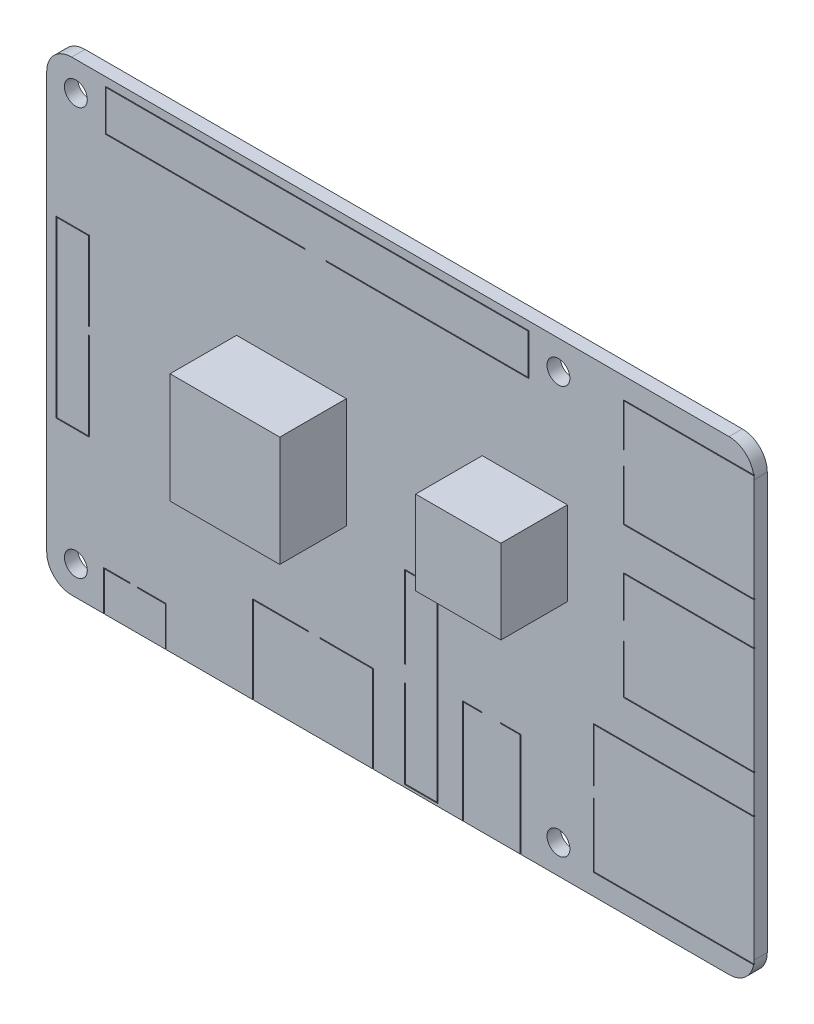
SolidWorks part; units mm, degrees
ref_plane "Front Plane" through (0, 0, 0) normal (0, 0, 1) x (1, 0, 0)
ref_plane "Top Plane" through (0, 0, 0) normal (0, 1, 0) x (1, 0, 0)
ref_plane "Right Plane" through (0, 0, 0) normal (1, 0, 0) x (0, 0, -1)
sketch "Sketch1" plane through (0, 0, 0) normal (0, 0, 1) x (1, 0, 0)
  line L1 (-39.5, -28) -> (39.5, -28)
  line L2 (-42.5, -25) -> (-42.5, 25)
  line L3 (-39.5, 28) -> (39.5, 28)
  line L4 (42.5, -25) -> (42.5, 25)
  line L5 (-42.5, -28) -> (42.5, 28) construction
  line L6 (-42.5, 28) -> (42.5, -28) construction
  arc A0 (-39.5, -28) -> (-42.5, -25) centre (-39.5, -25) cw
  arc A1 (39.5, -28) -> (42.5, -25) centre (39.5, -25) ccw
  arc A2 (39.5, 28) -> (42.5, 25) centre (39.5, 25) cw
  arc A3 (-42.5, 25) -> (-39.5, 28) centre (-39.5, 25) cw
  circle A4 centre (-39, 24.5) radius 1.375
  circle A5 centre (-39, -24.5) radius 1.375
  circle A6 centre (19, 24.5) radius 1.375
  circle A7 centre (19, -24.5) radius 1.375
  point P0 (0, 0)
  dimension "D3" = 3
  dimension "D4" = 2.75
  dimension "D5" = 3.5
  dimension "D6" = 3.5
  dimension "D7" = 58
  dimension "D8" = 58
  dimension "D9" = 49
  dimension "D12" = 49
  dimension "D1" = 85
  dimension "D2" = 56
  dimension "D10" = 24.5
  dimension "D11" = 24.5
extrude "Boss-Extrude1" add sketch "Sketch1" along normal blind 1.6
sketch "Sketch2" plane through (0, 0, 1.6) normal (0, 0, 1) x (1, 0, 0)
  line L1 (-42.5, 25) -> (-42.5, -25) construction
  line L2 (-35.65, -28.6369) -> (-28.15, -28.6369)
  line L3 (-35.65, -28.6369) -> (-35.65, -23.2)
  line L4 (-35.65, -23.2) -> (-32.465, -23.2)
  line L5 (-28.15, -28.6369) -> (-28.15, -23.2)
  line L6 (-35.65, -28.6369) -> (-28.15, -23.2) construction
  line L7 (-35.65, -23.2) -> (-28.15, -28.6369) construction
  line L8 (-39.5, -28) -> (39.5, -28) construction
  line L9 (-17.75, -17.5) -> (-11.0158, -17.5)
  line L10 (-17.75, -17.5) -> (-17.75, -33.1614)
  line L11 (-17.75, -33.1614) -> (-3.25, -33.1614)
  line L12 (-3.25, -17.5) -> (-3.25, -33.1614)
  line L13 (-17.75, -17.5) -> (-3.25, -33.1614) construction
  line L14 (-17.75, -33.1614) -> (-3.25, -17.5) construction
  line L15 (0.5, -5.3) -> (4.5, -5.3)
  line L16 (0.5, -5.3) -> (0.5, -15.174)
  line L17 (0.5, -27.7) -> (4.5, -27.7)
  line L18 (4.5, -5.3) -> (4.5, -27.7)
  line L19 (0.5, -5.3) -> (4.5, -27.7) construction
  line L20 (0.5, -27.7) -> (4.5, -5.3) construction
  line L21 (7.5, -15.5) -> (9.7992, -15.5)
  line L22 (7.5, -15.5) -> (7.5, -31.1614)
  line L23 (7.5, -31.1614) -> (14.5, -31.1614)
  line L24 (14.5, -15.5) -> (14.5, -31.1614)
  line L25 (7.5, -15.5) -> (14.5, -31.1614) construction
  line L26 (7.5, -31.1614) -> (14.5, -15.5) construction
  line L27 (-35.45, 27) -> (15.45, 27)
  line L28 (-35.45, 27) -> (-35.45, 22)
  line L29 (-35.45, 22) -> (-11.4582, 22)
  line L30 (15.45, 27) -> (15.45, 22)
  line L31 (-35.45, 27) -> (15.45, 22) construction
  line L32 (-35.45, 22) -> (15.45, 27) construction
  line L33 (-41.3717, -10.5142) -> (-37.3717, -10.5142)
  line L34 (-41.3717, -10.5142) -> (-41.3717, 10.5142)
  line L35 (-41.3717, 10.5142) -> (-37.3717, 10.5142)
  line L36 (-37.3717, -10.5142) -> (-37.3717, 0.0947)
  line L37 (-41.3717, -10.5142) -> (-37.3717, 10.5142) construction
  line L38 (-41.3717, 10.5142) -> (-37.3717, -10.5142) construction
  line L39 (42.5, -25) -> (42.5, 25) construction
  line L40 (23.2, -25.5) -> (44.7, -25.5)
  line L41 (23.2, -25.5) -> (23.2, -17.75)
  line L42 (23.2, -10) -> (44.7, -10)
  line L43 (44.7, -25.5) -> (44.7, -10)
  line L44 (23.2, -25.5) -> (44.7, -10) construction
  line L45 (23.2, -10) -> (44.7, -25.5) construction
  line L46 (26.8, -5.5) -> (54.0714, -5.5)
  line L47 (26.8, -5.5) -> (26.8, 0.4072)
  line L48 (26.8, 7.5) -> (54.0714, 7.5)
  line L49 (54.0714, -5.5) -> (54.0714, 7.5)
  line L50 (26.8, -5.5) -> (54.0714, 7.5) construction
  line L51 (26.8, 7.5) -> (54.0714, -5.5) construction
  line L52 (26.8, 12.5) -> (57.7137, 12.5)
  line L53 (26.8, 12.5) -> (26.8, 18.6113)
  line L54 (26.8, 25.5) -> (57.7137, 25.5)
  line L55 (57.7137, 12.5) -> (57.7137, 25.5)
  line L56 (26.8, 12.5) -> (57.7137, 25.5) construction
  line L57 (26.8, 25.5) -> (57.7137, 12.5) construction
  line L58 (-35.35, 22.1) -> (-11.4582, 22.1)
  line L59 (15.35, 26.9) -> (15.35, 22.1)
  line L60 (-35.35, 26.9) -> (15.35, 26.9)
  line L61 (-35.35, 26.9) -> (-35.35, 22.1)
  line L62 (-41.2717, 10.4142) -> (-37.4717, 10.4142)
  line L63 (-37.4717, -10.4142) -> (-37.4717, 0.0947)
  line L64 (-41.2717, -10.4142) -> (-37.4717, -10.4142)
  line L65 (-41.2717, -10.4142) -> (-41.2717, 10.4142)
  line L66 (-35.55, -28.5369) -> (-35.55, -23.3)
  line L67 (-35.55, -23.3) -> (-32.465, -23.3)
  line L68 (-28.25, -28.5369) -> (-28.25, -23.3)
  line L69 (-35.55, -28.5369) -> (-28.25, -28.5369)
  line L70 (-17.65, -17.6) -> (-17.65, -33.0614)
  line L71 (-17.65, -33.0614) -> (-3.35, -33.0614)
  line L72 (-3.35, -17.6) -> (-3.35, -33.0614)
  line L73 (-17.65, -17.6) -> (-11.0158, -17.6)
  line L74 (0.6, -5.4) -> (0.6, -15.174)
  line L75 (0.6, -27.6) -> (4.4, -27.6)
  line L76 (4.4, -5.4) -> (4.4, -27.6)
  line L77 (0.6, -5.4) -> (4.4, -5.4)
  line L78 (7.6, -15.6) -> (9.7992, -15.6)
  line L79 (14.4, -15.6) -> (14.4, -31.0614)
  line L80 (7.6, -31.0614) -> (14.4, -31.0614)
  line L81 (7.6, -15.6) -> (7.6, -31.0614)
  line L82 (23.3, -25.4) -> (23.3, -17.75)
  line L83 (23.3, -10.1) -> (44.6, -10.1)
  line L84 (44.6, -25.4) -> (44.6, -10.1)
  line L85 (23.3, -25.4) -> (44.6, -25.4)
  line L86 (26.9, -5.4) -> (53.9714, -5.4)
  line L87 (53.9714, -5.4) -> (53.9714, 7.4)
  line L88 (26.9, 7.4) -> (53.9714, 7.4)
  line L89 (26.9, -5.4) -> (26.9, 0.4072)
  line L90 (26.9, 12.6) -> (57.6137, 12.6)
  line L91 (57.6137, 12.6) -> (57.6137, 25.4)
  line L92 (26.9, 25.4) -> (57.6137, 25.4)
  line L93 (26.9, 12.6) -> (26.9, 18.6113)
  line L94 (-37.4717, 1) -> (-37.4717, 10.4142)
  line L95 (-37.4717, 1) -> (-37.3717, 1)
  line L96 (26.9, 20.2773) -> (26.9, 25.4)
  line L97 (-37.4717, 0.0947) -> (-37.3717, 0.0947)
  line L98 (26.9, 12.6) -> (26.9, 25.4) construction
  line L99 (-37.4717, -10.4142) -> (-37.4717, 10.4142) construction
  line L100 (-37.3717, 1) -> (-37.3717, 10.5142)
  line L101 (-37.3717, -10.5142) -> (-37.3717, 10.5142) construction
  line L102 (26.8, 20.2773) -> (26.9, 20.2773)
  line L103 (26.9, 2.5528) -> (26.9, 7.4)
  line L104 (26.8, 18.6113) -> (26.9, 18.6113)
  line L105 (26.9, -5.4) -> (26.9, 7.4) construction
  line L106 (26.8, 20.2773) -> (26.8, 25.5)
  line L107 (26.8, 12.5) -> (26.8, 25.5) construction
  line L108 (23.2, -16.5) -> (23.3, -16.5)
  line L109 (12.0626, -15.5) -> (14.5, -15.5)
  line L110 (23.2, -17.75) -> (23.3, -17.75)
  line L111 (7.5, -15.5) -> (14.5, -15.5) construction
  line L112 (26.8, 2.5528) -> (26.9, 2.5528)
  line L113 (23.2, -16.5) -> (23.2, -10)
  line L114 (26.8, 0.4072) -> (26.9, 0.4072)
  line L115 (23.2, -25.5) -> (23.2, -10) construction
  line L116 (-8.9067, 22.1) -> (15.35, 22.1)
  line L117 (-32.465, -23.2) -> (-32.465, -23.3)
  line L118 (-35.35, 22.1) -> (15.35, 22.1) construction
  line L119 (-31.5737, -23.2) -> (-31.5737, -23.3)
  line L120 (-31.5737, -23.3) -> (-28.25, -23.3)
  line L121 (-11.0158, -17.5) -> (-11.0158, -17.6)
  line L122 (-35.55, -23.3) -> (-28.25, -23.3) construction
  line L123 (-9.6849, -17.5) -> (-9.6849, -17.6)
  line L124 (0.5, -15.174) -> (0.6, -15.174)
  line L125 (-9.6849, -17.5) -> (-3.25, -17.5)
  line L126 (0.5, -17.125) -> (0.6, -17.125)
  line L127 (-17.75, -17.5) -> (-3.25, -17.5) construction
  line L128 (0.5, -17.125) -> (0.5, -27.7)
  line L129 (9.7992, -15.5) -> (9.7992, -15.6)
  line L130 (0.5, -5.3) -> (0.5, -27.7) construction
  line L131 (12.0626, -15.5) -> (12.0626, -15.6)
  line L132 (26.8, 2.5528) -> (26.8, 7.5)
  line L133 (26.8, -5.5) -> (26.8, 7.5) construction
  line L134 (23.3, -16.5) -> (23.3, -10.1)
  line L135 (23.3, -25.4) -> (23.3, -10.1) construction
  line L136 (12.0626, -15.6) -> (14.4, -15.6)
  line L137 (7.6, -15.6) -> (14.4, -15.6) construction
  line L138 (0.6, -17.125) -> (0.6, -27.6)
  line L139 (0.6, -5.4) -> (0.6, -27.6) construction
  line L140 (-9.6849, -17.6) -> (-3.35, -17.6)
  line L141 (-17.65, -17.6) -> (-3.35, -17.6) construction
  line L142 (-31.5737, -23.2) -> (-28.15, -23.2)
  line L143 (-35.65, -23.2) -> (-28.15, -23.2) construction
  line L145 (-11.4582, 22.1) -> (-11.4582, 22)
  line L147 (-8.9067, 22.1) -> (-8.9067, 22)
  line L148 (-8.9067, 22) -> (15.45, 22)
  line L149 (-35.45, 22) -> (15.45, 22) construction
  circle A0 centre (-39, 24.5) radius 1.375 construction
  point P0 (-31.9, -25.9184)
  point P7 (-10.5, -25.3307)
  point P12 (2.5, -16.5)
  point P17 (11, -23.3307)
  point P22 (-10, 24.5)
  point P29 (-39.3717, 0)
  point P36 (33.95, -17.75)
  point P41 (40.4357, 1)
  point P46 (42.2569, 19)
  dimension "D5" = 29
  dimension "D26" = 0
  dimension "D1" = 10.6
  dimension "D2" = 32
  dimension "D3" = 13
  dimension "D4" = 53.5
  dimension "D6" = 28
  dimension "D7" = 11.5
  dimension "D8" = 10.25
  dimension "D9" = 29
  dimension "D10" = 47
  dimension "D11" = 7.5
  dimension "D12" = 4.8
  dimension "D13" = 14.5
  dimension "D14" = 10.5
  dimension "D15" = 4
  dimension "D16" = 22.7
  dimension "D17" = 7
  dimension "D18" = 12.5
  dimension "D19" = 15.5
  dimension "D20" = 19.3
  dimension "D21" = 21.5
  dimension "D22" = 13
  dimension "D23" = 13
  dimension "D24" = 15.7
  dimension "D25" = 15.7
  dimension "D27" = 5
  dimension "D28" = 50.9
  dimension "D29" = 4
  dimension "D30" = 0.1
extrude "Cut-Extrude1" cut sketch "Sketch2" against normal blind 0.1
sketch "Эскиз1" plane through (0, 0, 1.6) normal (0, 0, 1) x (1, 0, 0)
  line L1 (-19.6804, -4.3046) -> (-6.489, -4.3046)
  line L2 (-19.6804, -4.3046) -> (-19.6804, 8.9499)
  line L3 (-19.6804, 8.9499) -> (-6.489, 8.9499)
  line L4 (-6.489, -4.3046) -> (-6.489, 8.9499)
extrude "Бобышка-Вытянуть1" add sketch "Эскиз1" along normal blind 8
sketch "Эскиз2" plane through (0, 0, 1.6) normal (0, 0, 1) x (1, 0, 0)
  line L1 (9.84, 1.1083) -> (20.0762, 1.1083)
  line L2 (9.84, 1.1083) -> (9.84, 11.1833)
  line L3 (9.84, 11.1833) -> (20.0762, 11.1833)
  line L4 (20.0762, 1.1083) -> (20.0762, 11.1833)
extrude "Бобышка-Вытянуть2" add sketch "Эскиз2" along normal blind 8
